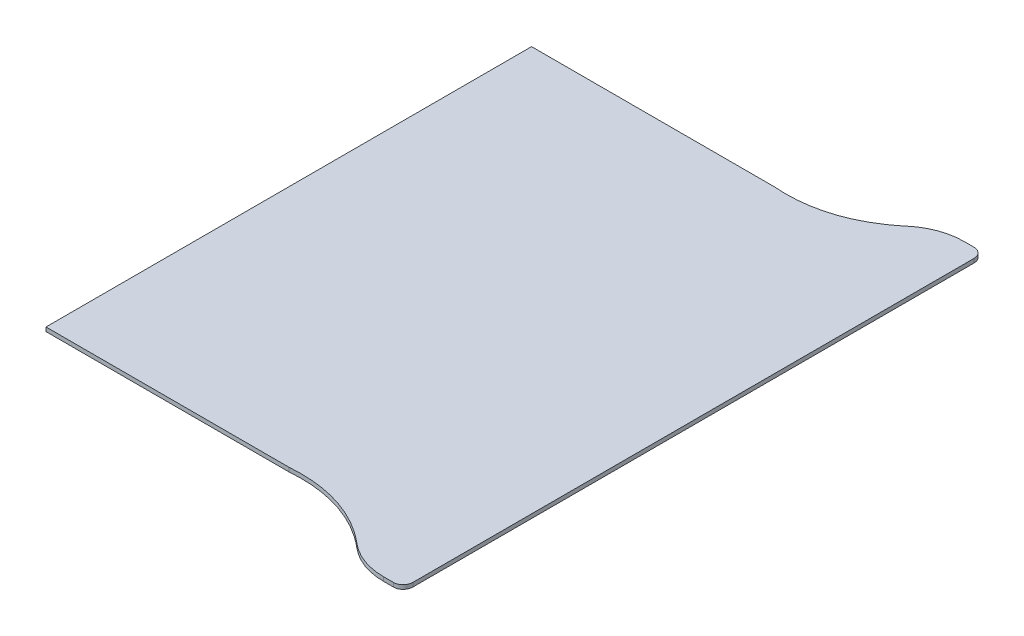
SolidWorks part; units mm, degrees
ref_plane "Front Plane" through (0, 0, 0) normal (0, 0, 1) x (1, 0, 0)
ref_plane "Top Plane" through (0, 0, 0) normal (0, 1, 0) x (1, 0, 0)
ref_plane "Right Plane" through (0, 0, 0) normal (1, 0, 0) x (0, 0, -1)
sketch "草图1" plane through (0, 0, 0) normal (0, 1, 0) x (1, 0, 0)
  line L0 (3.5, 3.4671) -> (3.5, -0.0136)
  line L1 (-1.5, 3) -> (1.5, 3)
  line L2 (-1.5, 3) -> (-1.5, -3)
  line L3 (-1.5, -3) -> (1.5, -3)
  line L4 (1.5, 3) -> (1.5, -3)
  line L5 (3.2569, 3.5871) -> (3.38, 3.5871)
  line L7 (-0.9141, 0) -> (0.9141, 0) construction
  line L8 (3.2569, -3.5871) -> (3.38, -3.5871)
  line L9 (3.5, -3.4671) -> (3.5, 0.0136)
  arc A0 (2.7401, 3.3979) -> (3.2569, 3.5871) centre (3.2569, 2.7871) cw
  arc A1 (3.38, 3.5871) -> (3.5, 3.4671) centre (3.38, 3.4671) cw
  arc A2 (3.38, -3.5871) -> (3.5, -3.4671) centre (3.38, -3.4671) ccw
  arc A3 (2.7401, -3.3979) -> (3.2569, -3.5871) centre (3.2569, -2.7871) ccw
  spline S0 degree 3 poles (1.5, 3) (1.9612, 2.9626) (2.3872, 3.0993) (2.7401, 3.3979) knots 0 0 0 0 0.839621 0.839621 0.839621 0.839621
  spline S1 degree 3 poles (1.5, -3) (1.9612, -2.9626) (2.3872, -3.0993) (2.7401, -3.3979) knots 0 0 0 0 0.839621 0.839621 0.839621 0.839621
  point P4 (-1.5, 0)
  point P6 (0, -3)
  dimension "D3" = 0.8
  dimension "D5" = 0.12
  dimension "D1" = 3
  dimension "D2" = 6
  dimension "D4" = 2
extrude "凸台-拉伸1" add sketch "草图1" along normal blind 0.05 contours L4 L1 L2 L3 | L4 S1 A3 L8 A2 L9 L0 A1 L5 A0 S0
